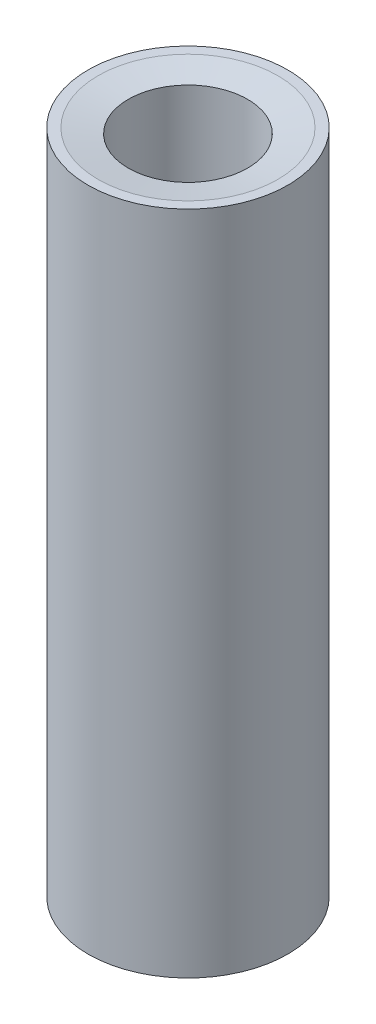
SolidWorks part; units mm, degrees
ref_plane "Front Plane" through (0, 0, 0) normal (0, 0, 1) x (1, 0, 0)
ref_plane "Top Plane" through (0, 0, 0) normal (0, 1, 0) x (1, 0, 0)
ref_plane "Right Plane" through (0, 0, 0) normal (1, 0, 0) x (0, 0, -1)
sketch "Sketch1" plane through (0, 0, 0) normal (0, 1, 0) x (1, 0, 0)
  circle A0 centre (0, 0) radius 2.3812
  dimension "D1" = 4.7625
extrude "Extrude1" add sketch "Sketch1" along normal blind 15.875
hole_wizard "#4-40 Tapped Hole1" positions "3DSketch1" profile "Sketch2" tap size "#4-40" standard "Ansi Inch"
sketch3d "3DSketch1"
  line L0 (0, 15.875, 0) -> (-0.5775, 15.875, -2.3102) construction
  line L1 (0, 15.875, 0) -> (0, 0, 0) construction
  line L2 (0, 0, 0) -> (-0.7779, 0, 2.2506) construction
  circle A0 centre (0, 15.875, 0) radius 2.3812 construction
  circle A1 centre (0, 0, 0) radius 2.3812 construction
  point P0 (0, 15.875, 0)
  point P10 (0, 18.2563, 0)
  point P13 (0, 0, 0)
  point P16 (0, 0, 0)
  point P21 (0, 2.3812, 0)
sketch "Sketch2" plane through (0, 15.875, 0) normal (1, 0, 0) x (0, 0, 1)
  line L0 (0, 0) -> (0, 8.2992)
  line L1 (0, 8.2992) -> (1.1303, 7.62)
  line L2 (1.1303, 7.62) -> (1.1303, 5.588)
  line L3 (1.1303, 5.588) -> (1.4224, 5.588)
  line L4 (1.4224, 5.588) -> (1.4224, 0)
  line L5 (1.4224, 0) -> (0, 0)
  line L10 (0, 8.2992) -> (-1.1303, 7.62) construction
  line L11 (0, -6.35) -> (0, 107.95) construction
  dimension "Tap Drill Dia." = 2.2606
  dimension "Tap Drill Depth" = 7.62
  dimension "Thread Major Dia." = 2.8448
  dimension "Thread Depth" = 5.588
  dimension "Drill Angle" = 118
chamfer "Chamfer1" distance 0.127 angle 80 1 edges at (0, 15.875, 1.4224)
